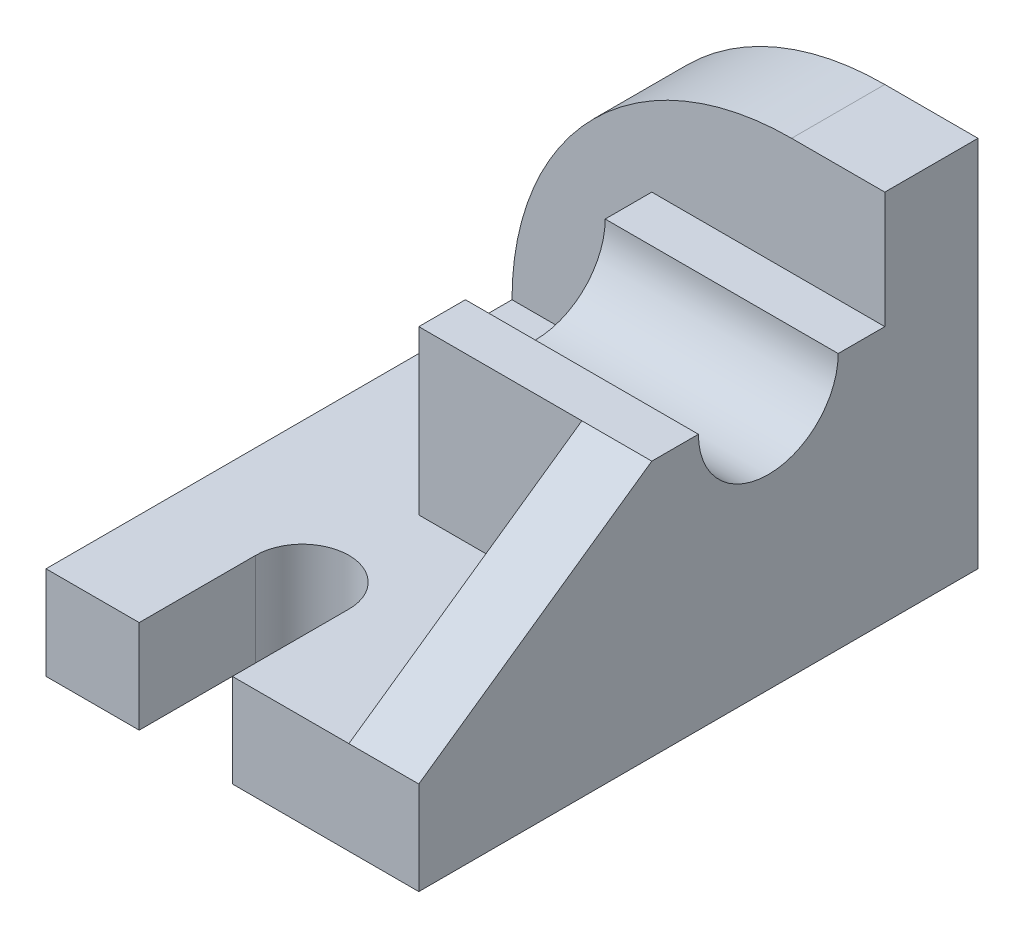
SolidWorks part; units mm, degrees
ref_plane "Front Plane" through (0, 0, 0) normal (0, 0, 1) x (1, 0, 0)
ref_plane "Top Plane" through (0, 0, 0) normal (0, 1, 0) x (1, 0, 0)
ref_plane "Right Plane" through (0, 0, 0) normal (1, 0, 0) x (0, 0, -1)
sketch "Sketch2" plane through (0, 0, 0) normal (0, 1, 0) x (1, 0, 0)
  line L1 (-32, 48) -> (32, 48)
  line L2 (-32, 48) -> (-32, -48)
  line L3 (-32, -48) -> (32, -48)
  line L4 (32, 48) -> (32, -48)
  point P0 (0, 0)
extrude "Boss-Extrude1" add sketch "Sketch2" along normal blind 16 contours L2 L1 L4 L3
sketch "Sketch3" plane through (0, 16, 0) normal (0, 1, 0) x (1, 0, 0)
  line L0 (32, 48) -> (32, -48) construction
  line L1 (-32, 48) -> (32, 48)
  line L2 (-32, 48) -> (-32, 32)
  line L3 (-32, 32) -> (32, 32)
  line L4 (32, 48) -> (32, 32)
  dimension "D1" = 16
extrude "Boss-Extrude3" add sketch "Sketch3" along normal blind 48 contours L2 L1 L4 L3
fillet "Fillet3" radius 48 1 edges at (-32, 64, -40)
sketch "Sketch5" plane through (0, 16, 0) normal (0, 1, 0) x (1, 0, 0)
  line L1 (32, 32) -> (-8, 32)
  line L2 (32, 32) -> (32, -8)
  line L3 (32, -8) -> (-8, -8)
  line L4 (-8, 32) -> (-8, -8)
  dimension "D1" = 40
extrude "Boss-Extrude4" add sketch "Sketch5" along normal blind 28
sketch "Sketch6" plane through (-8, 0, 0) normal (-1, 0, 0) x (0, 0, 1)
  line L0 (-32, 44) -> (8, 44) construction
  circle A0 centre (-12, 44) radius 12
extrude "Cut-Extrude1" cut sketch "Sketch6" against normal blind 63
sketch "Sketch7" plane through (0, 16, 0) normal (0, 1, 0) x (1, 0, 0)
  line L0 (-32, -48) -> (32, -48) construction
  line L1 (32, -8) -> (19.9978, -8)
  line L2 (32, -8) -> (32, -48)
  line L3 (32, -48) -> (19.9978, -48)
  line L4 (19.9978, -8) -> (19.9978, -48)
extrude "Boss-Extrude6" add sketch "Sketch7" along normal blind 28 contours L2 L1 L4 L3
sketch "Sketch9" plane through (19.9978, 0, 0) normal (-1, 0, 0) x (0, 0, 1)
  line L0 (8, 44) -> (48, 16)
  line L1 (48, 16) -> (48, 44)
  line L2 (48, 44) -> (8, 44)
extrude "Cut-Extrude2" cut sketch "Sketch9" against normal blind 30
sketch "Sketch10" plane through (0, 16, 0) normal (0, 1, 0) x (1, 0, 0)
  line L0 (-8, -48) -> (-8, -28) construction
  line L2 (-32, -48) -> (19.9978, -48) construction
  line L3 (-16, -48) -> (-16, -28)
  line L5 (0, -48) -> (0, -28)
  line L6 (-32, 32) -> (-32, -48) construction
  arc A0 (-16, -48) -> (0, -48) centre (-8, -48) ccw
  arc A1 (0, -28) -> (-16, -28) centre (-8, -28) ccw
  point P5 (-8, -38)
  dimension "D2" = 8
  dimension "D1" = 20
  dimension "D3" = 16
extrude "Cut-Extrude3" cut sketch "Sketch10" against normal through all contours A1 L3 A0 L5
